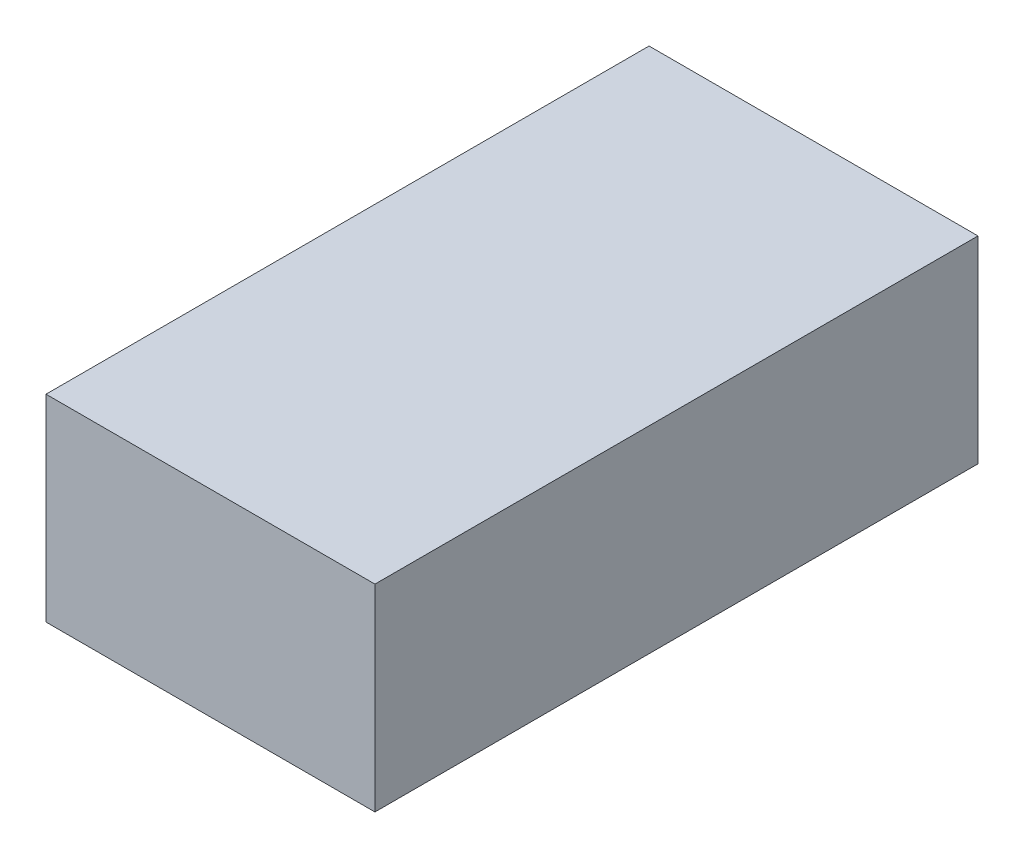
SolidWorks part; units mm, degrees
ref_plane "前视基准面" through (0, 0, 0) normal (0, 0, 1) x (1, 0, 0)
ref_plane "上视基准面" through (0, 0, 0) normal (0, 1, 0) x (1, 0, 0)
ref_plane "右视基准面" through (0, 0, 0) normal (1, 0, 0) x (0, 0, -1)
sketch "草图1" plane through (0, 0, 0) normal (0, 1, 0) x (1, 0, 0)
  line L1 (-15, -27.5) -> (15, -27.5)
  line L2 (-15, -27.5) -> (-15, 27.5)
  line L3 (-15, 27.5) -> (15, 27.5)
  line L4 (15, -27.5) -> (15, 27.5)
  line L5 (-15, -27.5) -> (15, 27.5) construction
  line L6 (-15, 27.5) -> (15, -27.5) construction
  point P0 (0, 0)
  dimension "D1" = 55
  dimension "D2" = 30
extrude "凸台-拉伸1" add sketch "草图1" along normal blind 18
